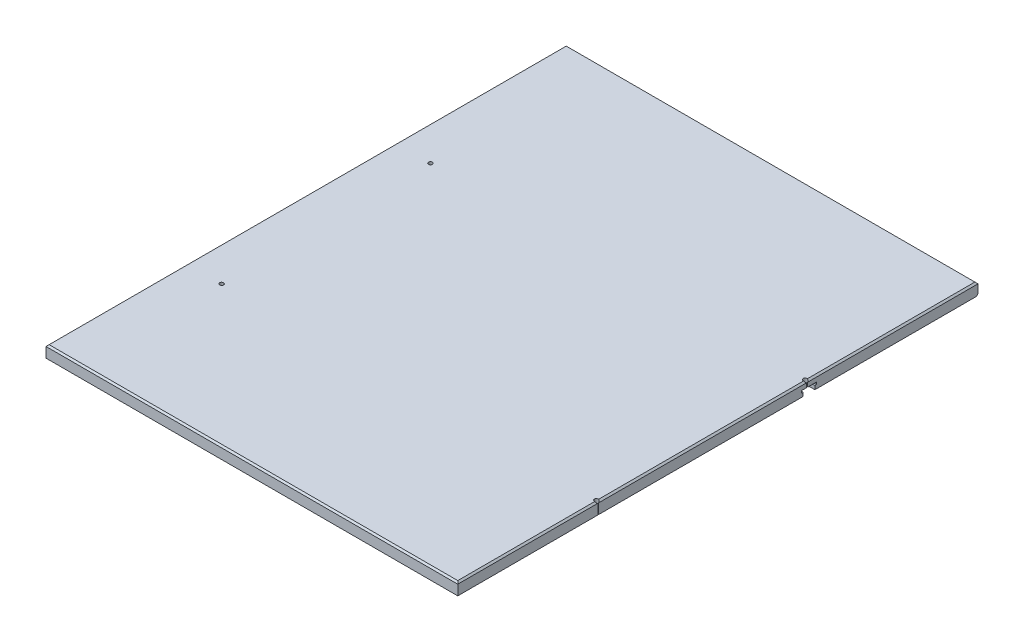
SolidWorks part; units mm, degrees
material "Oak"
ref_plane "Front Plane" through (0, 0, 0) normal (0, 0, 1) x (1, 0, 0)
ref_plane "Top Plane" through (0, 0, 0) normal (0, 1, 0) x (1, 0, 0)
ref_plane "Right Plane" through (0, 0, 0) normal (1, 0, 0) x (0, 0, -1)
sketch "Sketch1" plane through (0, 0, 0) normal (0, 1, 0) x (1, 0, 0)
  line L1 (0, 0) -> (669.8488, 0)
  line L2 (0, 0) -> (0, 846.328)
  line L3 (0, 846.328) -> (669.8488, 846.328)
  line L4 (669.8488, 0) -> (669.8488, 846.328)
  dimension "D1" = 846.328
  dimension "D2" = 669.8488
extrude "Boss-Extrude1" add sketch "Sketch1" along normal blind 19.05
chamfer "Chamfer1" distance 2.54 angle 45 4 edges at (334.9244, 19.05, -846.328) (669.8488, 19.05, -423.164) (334.9244, 19.05, 0) (0, 19.05, -423.164)
chamfer "Chamfer2" distance 2.54 angle 45 1 edges at (334.9244, 0, -846.328)
sketch "Sketch2" plane through (0, 19.05, 0) normal (0, 1, 0) x (1, 0, 0)
  line L1 (57.15, 568.325) -> (666.75, 568.325) construction
  line L2 (57.15, 568.325) -> (57.15, 228.6) construction
  line L3 (57.15, 228.6) -> (666.75, 228.6) construction
  line L4 (666.75, 568.325) -> (666.75, 228.6) construction
  circle A1 centre (57.15, 568.325) radius 3.175
  circle A3 centre (57.15, 228.6) radius 3.175
  circle A5 centre (666.75, 568.325) radius 3.175
  circle A7 centre (666.75, 228.6) radius 3.175
  dimension "D1" = 6.35
  dimension "D2" = 609.6
  dimension "D3" = 339.725
  dimension "D4" = 228.6
  dimension "D5" = 57.15
sketch "Sketch3" plane through (0, 0, 0) normal (-1, 0, 0) x (0, 0, 1)
  line L5 (-846.328, 16.51) -> (-846.328, 2.54)
  line L6 (-846.328, 2.54) -> (-843.788, 0)
  line L7 (-843.788, 0) -> (0, 0)
  line L8 (0, 0) -> (0, 16.51)
  line L9 (0, 16.51) -> (-846.328, 16.51)
  line L10 (-846.328, 16.51) -> (-846.328, 2.54)
  line L11 (-846.328, 2.54) -> (-843.788, 0)
  line L12 (-843.788, 0) -> (0, 0)
  line L13 (0, 0) -> (0, 16.51)
  line L14 (0, 16.51) -> (-846.328, 16.51)
  line L17 (-583.6006, 5.9753) -> (-583.6006, 9.5313)
  line L18 (-580.9336, 5.9753) -> (-583.6006, 5.9753)
  line L19 (-580.9336, 0) -> (-580.9336, 5.9753)
  line L20 (-561.8836, 5.9753) -> (-561.8836, 0)
  line L21 (-559.2166, 9.5313) -> (-559.2166, 5.9753)
  line L22 (-559.2166, 5.9753) -> (-561.8836, 5.9753)
  line L23 (-583.6006, 9.5313) -> (-559.2166, 9.5313)
  line L24 (-571.4086, 10.86) -> (-571.4086, -6.3519) construction
  line L25 (-580.9336, 0) -> (-561.8836, 0)
  dimension "D2" = 9.5313
  dimension "D3" = 5.9753
  dimension "D4" = 559.2166
  dimension "D5" = 24.384
  dimension "D6" = 19.05
  dimension "D1" = 0
extrude "Cut-Extrude2" cut sketch "Sketch3" against normal through all contours L24 L23 L17 L18 L19 L12 | L23 L24 L25 L20 L22 L21
extrude "Cut-Extrude3" cut sketch "Sketch2" against normal through all
